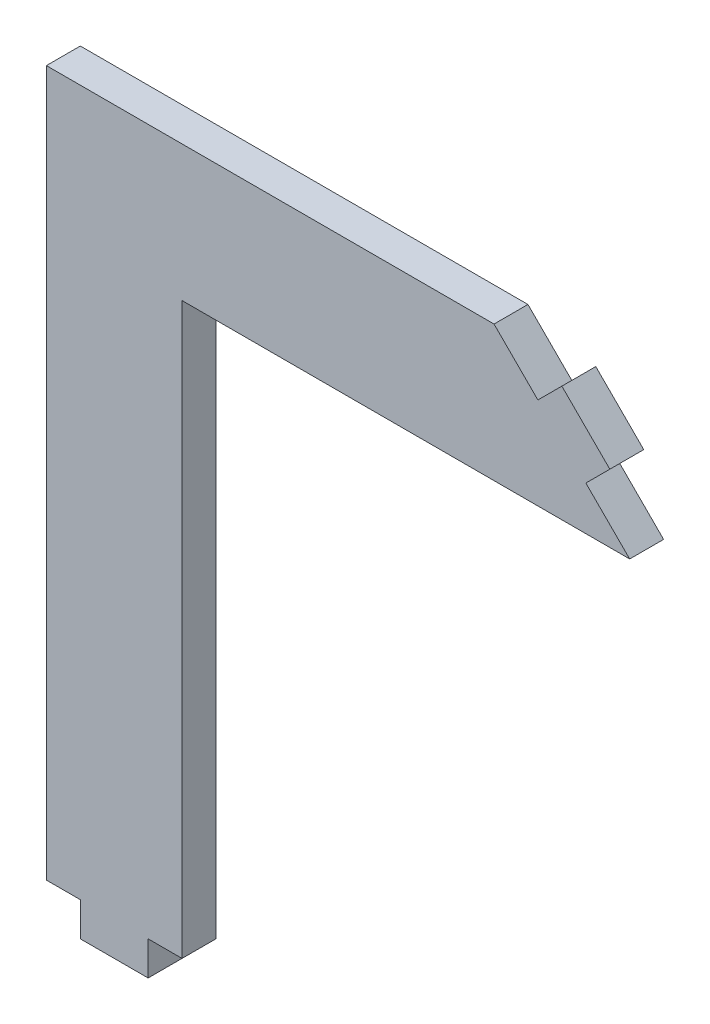
SolidWorks part; units mm, degrees
ref_plane "Front" through (0, 0, 0) normal (0, 0, 1) x (1, 0, 0)
ref_plane "Top" through (0, 0, 0) normal (0, 1, 0) x (1, 0, 0)
ref_plane "Right" through (0, 0, 0) normal (1, 0, 0) x (0, 0, -1)
sketch "Sketch1" plane through (0, 0, 0) normal (0, 0, 1) x (1, 0, 0)
  line L1 (0, 0) -> (12.7, 0)
  line L2 (0, 0) -> (0, -12.7)
  line L3 (0, -12.7) -> (12.7, -12.7)
  line L4 (12.7, 0) -> (12.7, -12.7)
  dimension "D1" = 12.7
  dimension "D2" = 12.7
extrude "Boss-Extrude1" add sketch "Sketch1" along normal blind 3.175
sketch "Sketch3" plane through (0, 0, 0) normal (0, 0, -1) x (-1, 0, 0)
  line L0 (0, 0) -> (-12.7, -12.7)
  line L1 (-12.7, -12.7) -> (-12.7, 0) construction
  line L2 (-12.7, -12.7) -> (-12.7, 0)
  line L3 (-12.7, 0) -> (0, 0)
  dimension "D1" = 45
extrude "Cut-Extrude1" cut sketch "Sketch3" against normal through all
sketch "Sketch4" plane through (0, 0, 0) normal (0.7071, 0.7071, 0) x (0, 0, -1)
  line L0 (-3.175, -8.9803) -> (0, -8.9803) construction
  line L1 (-3.175, -17.9605) -> (-3.175, 0) construction
  line L2 (0, -17.9605) -> (0, 0) construction
  line L4 (-3.175, -5.8053) -> (0, -5.8053)
  line L5 (-3.175, -5.8053) -> (-3.175, -12.1553)
  line L6 (-3.175, -12.1553) -> (0, -12.1553)
  line L7 (0, -5.8053) -> (0, -12.1553)
  dimension "D1" = 6.35
  dimension "D2" = 3.175
extrude "Boss-Extrude3" add sketch "Sketch4" along normal blind 3.175
sketch "Sketch5" plane through (0, 0, 0) normal (-1, 0, 0) x (0, 0, 1)
  line L1 (0, -12.7) -> (3.175, -12.7)
  line L2 (0, -12.7) -> (0, 0)
  line L3 (0, 0) -> (3.175, 0)
  line L4 (3.175, -12.7) -> (3.175, 0)
extrude "Boss-Extrude4" add sketch "Sketch5" along normal blind 41.91
sketch "Sketch6" plane through (0, -12.7, 0) normal (0, -1, 0) x (-1, 0, 0)
  line L0 (41.91, -3.175) -> (-12.7, -3.175) construction
  line L1 (29.21, -3.175) -> (41.91, -3.175)
  line L2 (29.21, -3.175) -> (29.21, 0)
  line L3 (29.21, 0) -> (41.91, 0)
  line L4 (41.91, -3.175) -> (41.91, 0)
  dimension "D1" = 12.7
extrude "Boss-Extrude5" add sketch "Sketch6" along normal blind 53.34
sketch "Sketch7" plane through (0, -66.04, 0) normal (0, -1, 0) x (1, 0, 0)
  line L0 (-35.56, 0) -> (-35.56, 3.175) construction
  line L1 (-41.91, 0) -> (-29.21, 0) construction
  line L2 (-29.21, 3.175) -> (-41.91, 3.175) construction
  line L4 (-32.385, 3.175) -> (-38.735, 3.175)
  line L5 (-32.385, 3.175) -> (-32.385, 0)
  line L6 (-32.385, 0) -> (-38.735, 0)
  line L7 (-38.735, 3.175) -> (-38.735, 0)
  line L8 (-32.385, 3.175) -> (-38.735, 0) construction
  line L9 (-32.385, 0) -> (-38.735, 3.175) construction
  point P6 (-35.56, 1.5875)
  dimension "D1" = 6.35
extrude "Boss-Extrude6" add sketch "Sketch7" along normal blind 3.175
